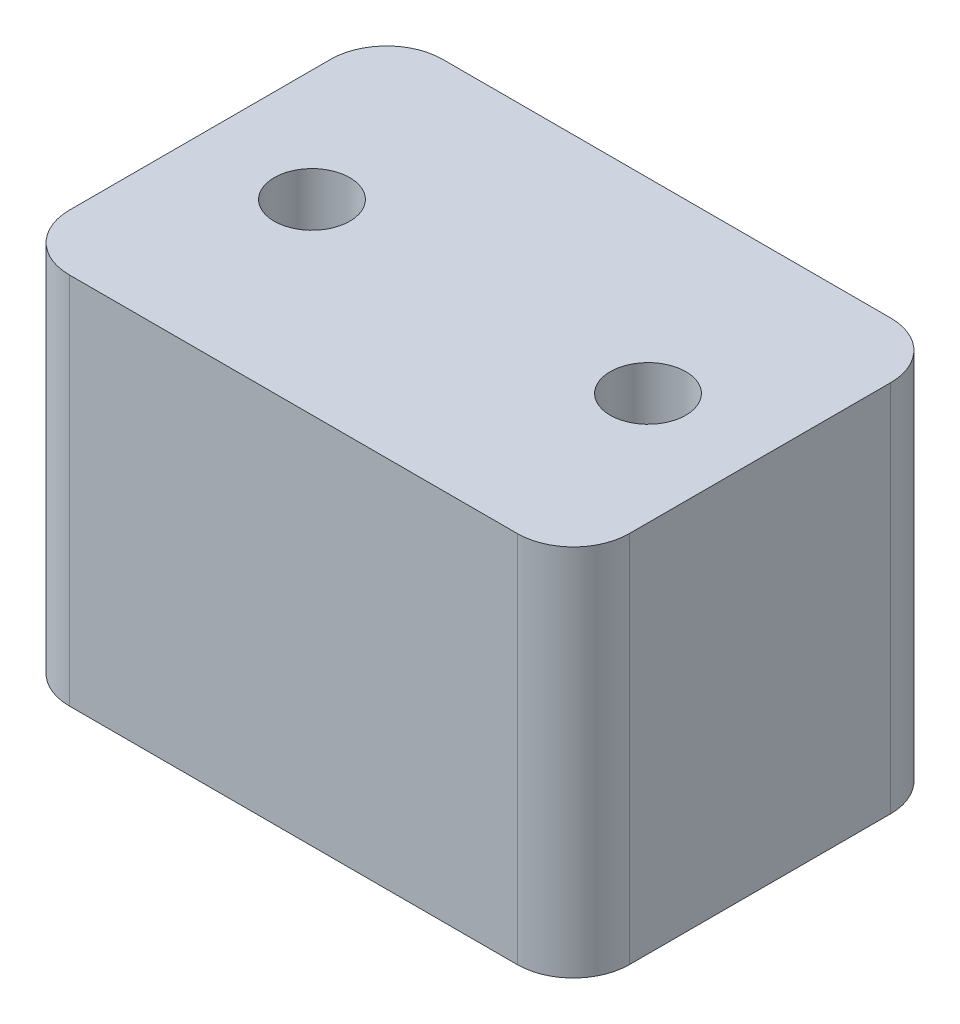
SolidWorks part; units mm, degrees
ref_plane "前视基准面" through (0, 0, 0) normal (0, 0, 1) x (1, 0, 0)
ref_plane "上视基准面" through (0, 0, 0) normal (0, 1, 0) x (1, 0, 0)
ref_plane "右视基准面" through (0, 0, 0) normal (1, 0, 0) x (0, 0, -1)
other "Configuration Table"
sketch "草图1" plane through (0, 0, 0) normal (0, 1, 0) x (1, 0, 0)
  line L1 (-15, -10) -> (15, -10)
  line L2 (-15, -10) -> (-15, 10)
  line L3 (-15, 10) -> (15, 10)
  line L4 (15, -10) -> (15, 10)
  line L5 (-15, -10) -> (15, 10) construction
  line L6 (-15, 10) -> (15, -10) construction
  point P0 (0, 0)
  dimension "D1" = 20
  dimension "D2" = 30
extrude "凸台-拉伸1" add sketch "草图1" along normal blind 20
sketch "草图2" plane through (0, 20, 0) normal (0, 1, 0) x (1, 0, 0)
  line L0 (0, 0) -> (0, 10) construction
  line L1 (15, 10) -> (-15, 10) construction
  circle A0 centre (-9, 0) radius 2.025
  circle A1 centre (9, 0) radius 2.025
  dimension "D2" = 4.05
  dimension "D1" = 18
extrude "切除-拉伸1" cut sketch "草图2" against normal blind 20
fillet "圆角1" radius 3 4 edges at (-15, 10, 10) (-15, 10, -10) (15, 10, -10) (15, 10, 10)
